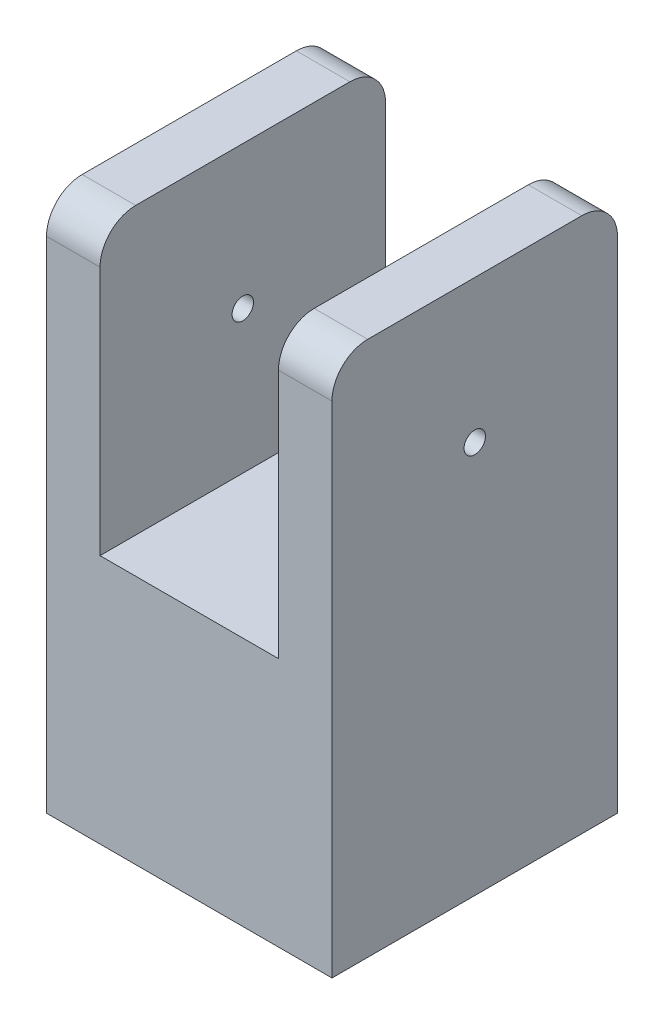
SolidWorks part; units mm, degrees
material "ABS"
ref_plane "Front Plane" through (0, 0, 0) normal (0, 0, 1) x (1, 0, 0)
ref_plane "Top Plane" through (0, 0, 0) normal (0, 1, 0) x (1, 0, 0)
ref_plane "Right Plane" through (0, 0, 0) normal (1, 0, 0) x (0, 0, -1)
sketch "Sketch1" plane through (0, 0, 0) normal (0, 1, 0) x (1, 0, 0)
  line L1 (-40, -40) -> (40, -40)
  line L2 (-40, -40) -> (-40, 40)
  line L3 (-40, 40) -> (40, 40)
  line L4 (40, -40) -> (40, 40)
  line L5 (-40, -40) -> (40, 40) construction
  line L6 (-40, 40) -> (40, -40) construction
  circle A0 centre (0, 0) radius 3
  point P0 (0, 0)
  dimension "D3" = 6
  dimension "D1" = 80
  dimension "D2" = 80
extrude "Boss-Extrude1" add sketch "Sketch1" along normal blind 150
sketch "Sketch2" plane through (0, 150, 0) normal (0, 1, 0) x (1, 0, 0)
  line L0 (40, 40) -> (-40, 40) construction
  line L1 (25, -40) -> (-25, -40)
  line L2 (25, -40) -> (25, 40)
  line L3 (25, 40) -> (-25, 40)
  line L4 (-25, -40) -> (-25, 40)
  line L5 (25, -40) -> (-25, 40) construction
  line L6 (25, 40) -> (-25, -40) construction
  point P0 (0, 0)
  dimension "D1" = 50
extrude "Cut-Extrude1" cut sketch "Sketch2" against normal blind 80
sketch "Sketch3" plane through (40, 0, 0) normal (1, 0, 0) x (0, 0, -1)
  line L0 (40, 70) -> (-40, 70) construction
  line L1 (40, 70) -> (-40, 70) construction
  line L2 (-40, 150) -> (-40, 70) construction
  circle A0 centre (0, 110) radius 3
  point P8 (-40, 110)
  point P10 (0, 70)
  dimension "D1" = 6
extrude "Cut-Extrude2" cut sketch "Sketch3" against normal through all both and the other way through all
fillet "Fillet1" radius 10 4 edges at (-32.5, 150, -40) (32.5, 150, -40) (-32.5, 150, 40) (32.5, 150, 40)
